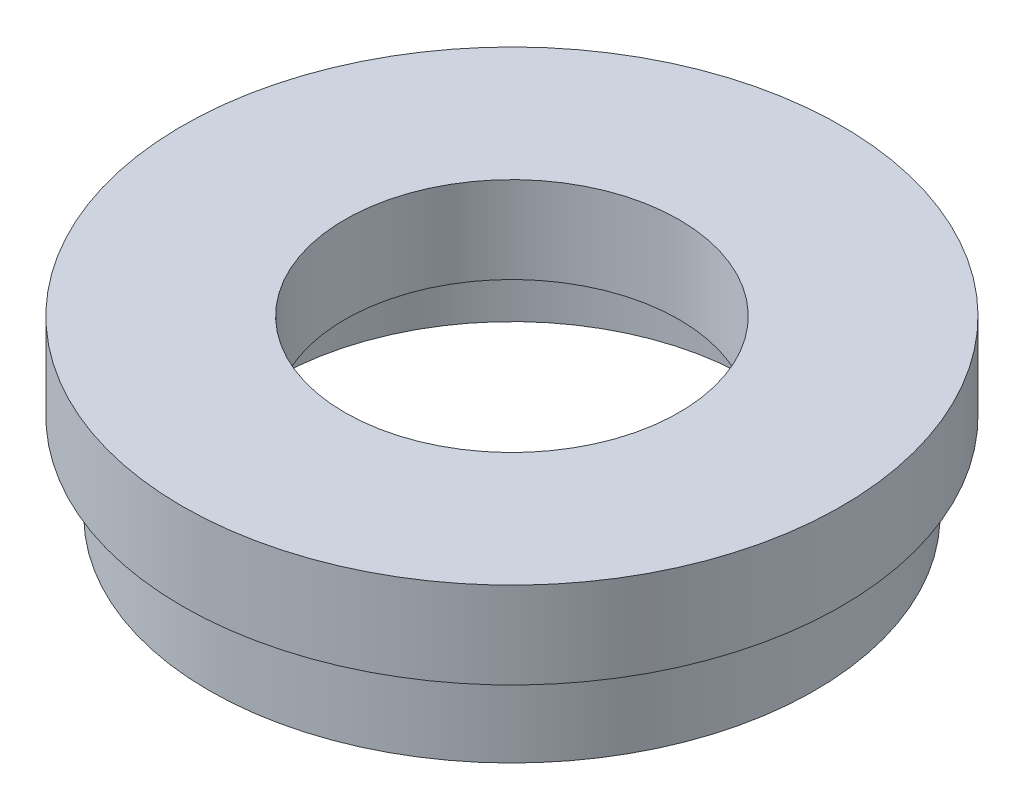
SolidWorks part; units mm, degrees
ref_plane "前视基准面" through (0, 0, 0) normal (0, 0, 1) x (1, 0, 0)
ref_plane "上视基准面" through (0, 0, 0) normal (0, 1, 0) x (1, 0, 0)
ref_plane "右视基准面" through (0, 0, 0) normal (1, 0, 0) x (0, 0, -1)
sketch "草图1" plane through (0, 0, 0) normal (0, 0, 1) x (1, 0, 0)
  line L0 (0, 13.7447) -> (0, -18.6809) construction
  line L1 (17.5, 0) -> (13.75, 0)
  line L2 (13.75, 0) -> (13.75, 4)
  line L3 (13.75, 4) -> (14.35, 4)
  line L4 (14.35, 4) -> (14.35, 5)
  line L5 (14.35, 5) -> (9.66, 5)
  line L6 (9.66, 5) -> (9.66, 10)
  line L7 (9.66, 10) -> (19.05, 10)
  line L8 (19.05, 10) -> (19.05, 5)
  line L9 (19.05, 5) -> (17, 5)
  line L10 (17, 5) -> (17, 4)
  line L11 (17, 4) -> (17.5, 4)
  line L12 (17.5, 4) -> (17.5, 0)
  dimension "D1" = 10
  dimension "D2" = 19.05
  dimension "D3" = 9.66
  dimension "D4" = 13.75
  dimension "D5" = 14.35
  dimension "D6" = 17.5
  dimension "D7" = 17
  dimension "D8" = 1
  dimension "D9" = 1
  dimension "D10" = 5
  dimension "D11" = 5
revolve "旋转1" add sketch "草图1" angle 360 about L0
cosmetic thread "装饰螺纹线1" parameters "D2"=20.32
cosmetic thread "装饰螺纹线2" parameters "D2"=28.5
cosmetic thread "装饰螺纹线3" parameters "D2"=34
